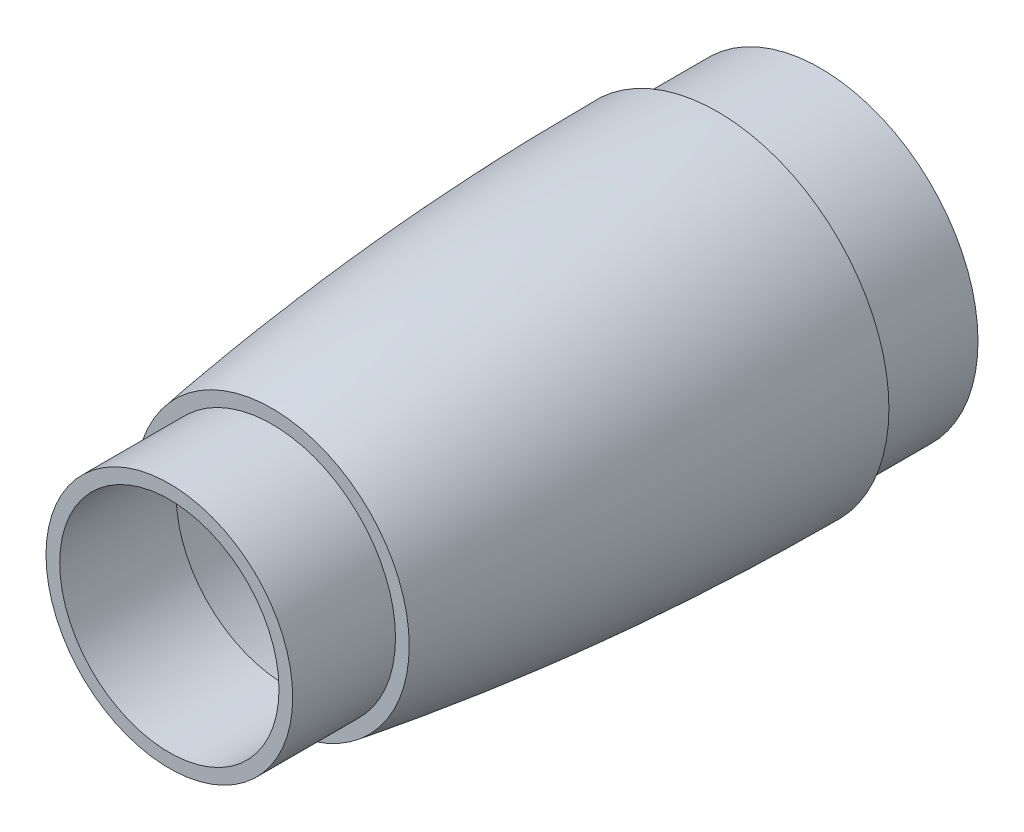
SolidWorks part; units mm, degrees
ref_plane "Front Plane" through (0, 0, 0) normal (0, 0, 1) x (1, 0, 0)
ref_plane "Top Plane" through (0, 0, 0) normal (0, 1, 0) x (1, 0, 0)
ref_plane "Right Plane" through (0, 0, 0) normal (1, 0, 0) x (0, 0, -1)
sketch "Sketch3" plane through (0, 0, 0) normal (1, 0, 0) x (0, 0, -1)
  line L0 (15, 20) -> (15, 18)
  line L1 (15, 18) -> (0, 18)
  line L2 (80, 25) -> (80, 23)
  line L3 (80, 23) -> (95, 23)
  line L4 (17, 16) -> (0, 16)
  line L5 (17, 18.2822) -> (17, 16)
  line L6 (78, 22.9953) -> (78, 21)
  line L7 (78, 21) -> (95, 21)
  line L8 (0, 16) -> (0, 18)
  line L9 (95, 21) -> (95, 23)
  line L10 (0, 0) -> (80, 0) construction
  spline S0 degree 10 poles (8.5615, 18.9529) (16.3554, 20.2819) (24.1492, 21.4451) (31.9431, 22.4445) (39.7369, 23.2817) (47.5308, 23.958) (55.3246, 24.4743) (63.1185, 24.8315) (70.9123, 25.0299) (78.7062, 25.0695) (86.5, 24.9503) knots 0 0 0 0 0 0 0 0 0 0 0 1 1 1 1 1 1 1 1 1 1 1 construction
  spline S1 degree 10 poles (15, 20) (21.5, 21.006) (28, 21.8975) (34.5, 22.6755) (41, 23.3411) (47.5, 23.8947) (54, 24.3371) (60.5, 24.6686) (67, 24.8895) (73.5, 25) (80, 25) knots 0.08261 0.08261 0.08261 0.08261 0.08261 0.08261 0.08261 0.08261 0.08261 0.08261 0.08261 0.916601 0.916601 0.916601 0.916601 0.916601 0.916601 0.916601 0.916601 0.916601 0.916601 0.916601
  spline S2 degree 1 poles (17, 18.2822) (78, 22.9953) knots 0 0 1 1 construction
  spline S3 degree 3 poles (17, 18.2822) (22.0703, 19.0459) (32.2561, 20.3905) (47.4982, 21.8418) (62.7511, 22.74) (72.9154, 22.9712) (78, 22.9953) knots 0.104449 0.104449 0.104449 0.104449 0.301041 0.497634 0.694226 0.890818 0.890818 0.890818 0.890818
  dimension "D1" = 15
  dimension "D2" = 15
  dimension "D3" = 2
  dimension "D4" = 2
  dimension "D5" = 15
  dimension "D6" = 18
  dimension "D7" = 25
  dimension "D8" = 2
revolve "Revolve1" add sketch "Sketch3" angle 360 about L10
equation "\"fr\"= 2cm"
equation "\"br\"= 2.5cm"
equation "\"l\"= 6.5cm"
equation "\"rho\" = ( ( \"br\" - \"fr\" ) ^ 2 + \"l\" ^ 2 )"
equation "\"Tl\" = ( \"br\" * ( \"l\" ^ 2 / ( \"br\" - \"fr\" ) - \"fr\" ) ) ^ ( 0.5 )"
